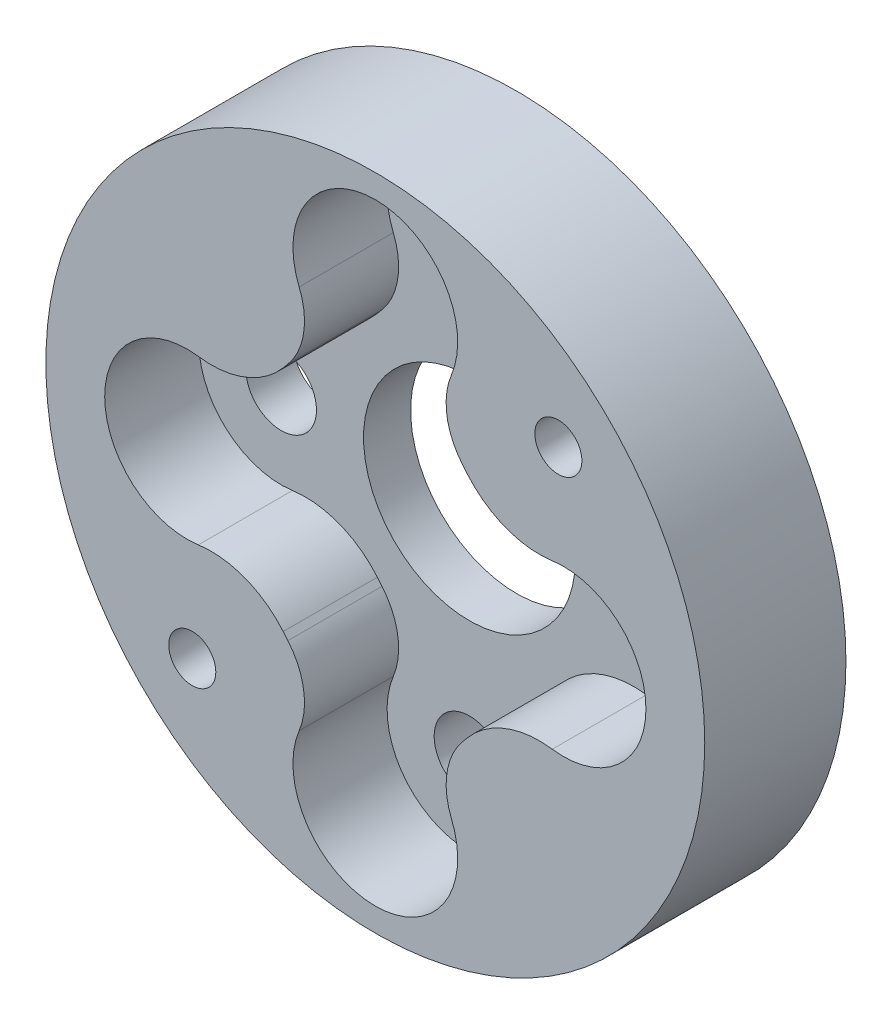
SolidWorks part; units mm, degrees
ref_plane "前视基准面" through (0, 0, 0) normal (0, 0, 1) x (1, 0, 0)
ref_plane "上视基准面" through (0, 0, 0) normal (0, 1, 0) x (1, 0, 0)
ref_plane "右视基准面" through (0, 0, 0) normal (1, 0, 0) x (0, 0, -1)
sketch "草图1" plane through (0, 0, 0) normal (0, 0, 1) x (1, 0, 0)
  line L0 (-115.0711, 0) -> (115.0711, 0) construction
  line L1 (0, -97.4334) -> (0, 97.4334) construction
  circle A0 centre (0, 0) radius 14
  point P6 (0, 0)
  dimension "D1" = 28
extrude "凸台-拉伸1" add sketch "草图1" along normal blind 2
sketch "草图2" plane through (0, 0, 2) normal (0, 0, 1) x (1, 0, 0)
  line L0 (-18.9001, 0) -> (20.2824, 0) construction
  line L1 (0, 19.9241) -> (0, -20.3452) construction
  circle A0 centre (-8, 0) radius 1.5
  circle A1 centre (0, 9.5) radius 1.5
  circle A2 centre (8, 0) radius 1.5
  circle A3 centre (0, -9.5) radius 1.5
  circle A5 centre (0, 0) radius 4.5
  dimension "D1" = 3
  dimension "D2" = 3
  dimension "D3" = 19
  dimension "D5" = 9
  dimension "D4" = 16
extrude "切除-拉伸1" cut sketch "草图2" against normal through all
sketch "草图3" plane through (0, 0, 2) normal (0, 0, 1) x (1, 0, 0)
  line L0 (-19.367, -19.367) -> (27.5176, 27.5176) construction
  line L1 (-33.1305, 0) -> (39.2818, 0) construction
  line L2 (25.347, -25.347) -> (-27.6313, 27.6313) construction
  line L3 (0, 37.257) -> (0, -42.5178) construction
  line L8 (-3.9134, -4.8528) -> (-3.7143, -5.0893)
  line L9 (3.7143, -5.0893) -> (3.9134, -4.8528)
  line L10 (3.9134, 4.8528) -> (3.7143, 5.0893)
  line L11 (-3.7143, 5.0893) -> (-3.9134, 4.8528)
  circle A0 centre (0, 0) radius 14
  circle A1 centre (-7.7782, -7.7782) radius 1
  circle A2 centre (7.7782, 7.7782) radius 1
  arc A16 (-7.5208, -3.467) -> (-3.9134, -4.8528) centre (-6.9731, -7.4294) cw
  arc A17 (-7.5208, 3.467) -> (-7.5208, -3.467) centre (-8, 0) ccw
  arc A18 (-3.2356, -8.1655) -> (3.2356, -8.1655) centre (0, -9.5) ccw
  arc A19 (7.5208, 3.467) -> (7.5208, -3.467) centre (8, 0) cw
  arc A20 (-3.2356, 8.1655) -> (3.2356, 8.1655) centre (0, 9.5) cw
  arc A21 (3.9134, -4.8528) -> (7.5208, -3.467) centre (6.9731, -7.4294) cw
  arc A22 (3.9134, 4.8528) -> (7.5208, 3.467) centre (6.9731, 7.4294) ccw
  arc A23 (-3.9134, 4.8528) -> (-7.5208, 3.467) centre (-6.9731, 7.4294) cw
  arc A24 (-3.7143, -5.0893) -> (-3.2356, -8.1655) centre (-6.009, -7.0217) cw
  arc A25 (3.2356, -8.1655) -> (3.7143, -5.0893) centre (6.009, -7.0217) cw
  arc A26 (3.7143, 5.0893) -> (3.2356, 8.1655) centre (6.009, 7.0217) cw
  arc A27 (-3.2356, 8.1655) -> (-3.7143, 5.0893) centre (-6.009, 7.0217) cw
  dimension "D1" = 28
  dimension "D3" = 2
  dimension "D5" = 7
  dimension "D6" = 7
  dimension "D7" = 4
  dimension "D8" = 3
  dimension "D2" = 45
  dimension "D4" = 22
extrude "凸台-拉伸3" add sketch "草图3" along normal blind 4
sketch "草图4" plane through (0, 0, 6) normal (0, 0, 1) x (1, 0, 0)
  circle A0 centre (7.7782, 7.7782) radius 1
  circle A1 centre (-7.7782, -7.7782) radius 1
extrude "切除-拉伸2" cut sketch "草图4" against normal through all
